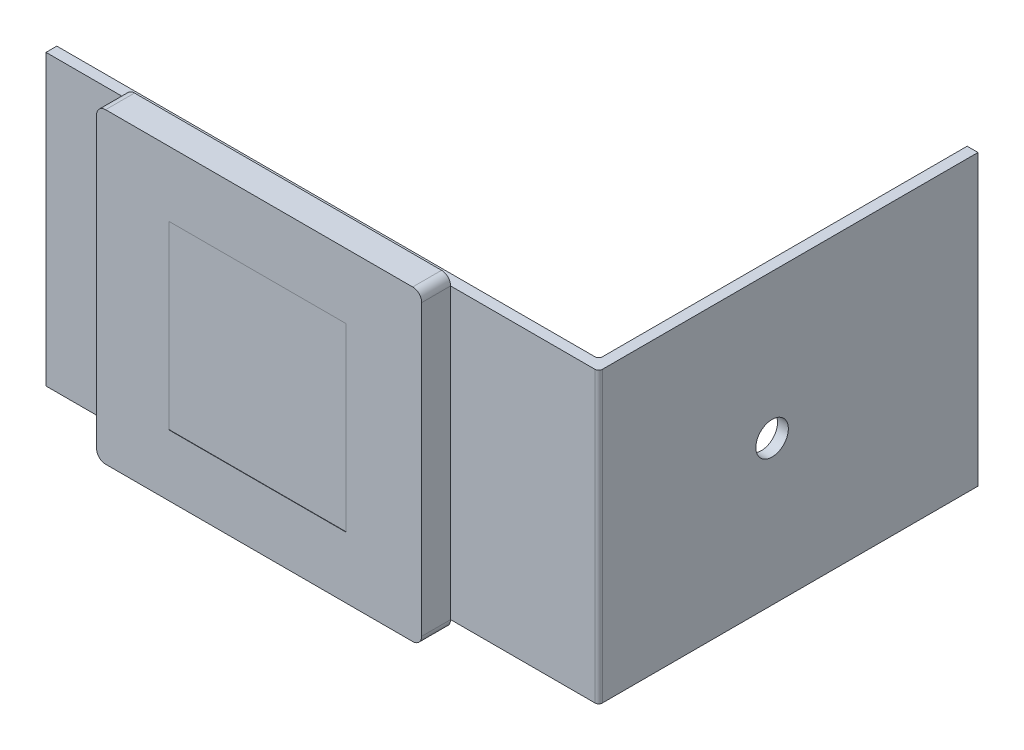
SolidWorks part; units mm, degrees
ref_plane "Ebene vorne" through (0, 0, 0) normal (0, 0, 1) x (1, 0, 0)
ref_plane "Ebene oben" through (0, 0, 0) normal (0, 1, 0) x (1, 0, 0)
ref_plane "Ebene rechts" through (0, 0, 0) normal (1, 0, 0) x (0, 0, -1)
sketch "Skizze1" plane through (0, 0, 0) normal (0, 1, 0) x (1, 0, 0)
  line L0 (-154.7975, -7.5838) -> (-154.7975, -10.5838)
  line L1 (-154.7975, -10.5838) -> (-2.7975, -10.5838)
  line L2 (-1.7975, -9.5838) -> (-1.7975, 94.4162)
  line L3 (-1.7975, 94.4162) -> (-4.7975, 94.4162)
  line L4 (-4.7975, 94.4162) -> (-4.7975, -6.5838)
  line L5 (-5.7975, -7.5838) -> (-154.7975, -7.5838)
  arc A0 (-4.7975, -6.5838) -> (-5.7975, -7.5838) centre (-5.7975, -6.5838) cw
  arc A1 (-2.7975, -10.5838) -> (-1.7975, -9.5838) centre (-2.7975, -9.5838) ccw
  dimension "D1" = 1
  dimension "D2" = 1
  dimension "D3" = 3
  dimension "D4" = 150
  dimension "D5" = 102
extrude "Aufsatz-Linear austragen1" add sketch "Skizze1" along normal blind 80
sketch "Skizze2" plane through (0, 0, 10.5838) normal (0, 0, 1) x (1, 0, 0)
  line L0 (-154.7975, 0) -> (-2.7975, 0) construction
  line L1 (-45.2975, -2.5) -> (-130.2975, -2.5)
  line L2 (-42.7975, 0) -> (-42.7975, 80)
  line L3 (-45.2975, 82.5) -> (-130.2975, 82.5)
  line L4 (-132.7975, 0) -> (-132.7975, 80)
  line L5 (-1.7975, 80) -> (-1.7975, 0) construction
  line L6 (-154.7975, 80) -> (-2.7975, 80) construction
  arc A0 (-45.2975, -2.5) -> (-42.7975, 0) centre (-45.2975, 0) ccw
  arc A1 (-130.2975, -2.5) -> (-132.7975, 0) centre (-130.2975, 0) cw
  arc A2 (-42.7975, 80) -> (-45.2975, 82.5) centre (-45.2975, 80) ccw
  arc A3 (-130.2975, 82.5) -> (-132.7975, 80) centre (-130.2975, 80) ccw
  point P8 (-42.7975, 0)
  dimension "D1" = 2.5
  dimension "D2" = 41
  dimension "D3" = 90
  dimension "D4" = 85
  dimension "D5" = 2.5
extrude "Aufsatz-Linear austragen2" add sketch "Skizze2" along normal blind 8
sketch "Skizze3" plane through (0, 0, 18.5838) normal (0, 0, 1) x (1, 0, 0)
  line L0 (-42.7975, 0) -> (-42.7975, 80) construction
  line L1 (-112.7975, 64.5) -> (-63.7975, 64.5)
  line L2 (-112.7975, 64.5) -> (-112.7975, 14.5)
  line L3 (-112.7975, 14.5) -> (-63.7975, 14.5)
  line L4 (-63.7975, 64.5) -> (-63.7975, 14.5)
  line L5 (-130.2975, -2.5) -> (-45.2975, -2.5) construction
  dimension "D1" = 49
  dimension "D2" = 21
  dimension "D3" = 17
  dimension "D4" = 50
extrude "Aufsatz-Linear austragen4" add sketch "Skizze3" against normal blind 0.1 and the other way blind 0.5 separate body contours L1 L4 L3 L2
combine bodies "Kombinieren1" operation type subtract main body 102 bodies to subtract 104
hole_wizard "Durchgangsloch für M81" positions "Skizze8" profile "Skizze9" hole size "M8" standard "ANSI Metrisch"
sketch "Skizze8" plane through (-1.7975, 0, 0) normal (1, 0, 0) x (0, 0, -1)
  line L0 (-9.5838, 80) -> (94.4162, 80) construction
  line L1 (-9.5838, 80) -> (-9.5838, 0) construction
  point P0 (37.4162, 40)
  dimension "D1" = 40
  dimension "D2" = 47
sketch "Skizze9" plane through (-1.7975, 40, -37.4162) normal (0, 1, 0) x (0, 0, -1)
  line L0 (0, 0) -> (0, 5.7029)
  line L1 (0, 5.7029) -> (4.5, 2.999)
  line L2 (4.5, 2.999) -> (4.5, 0)
  line L5 (4.5, 0) -> (0, 0)
  line L10 (0, 5.7029) -> (-4.5, 2.999) construction
  line L11 (0, -6.35) -> (0, 107.95) construction
  dimension "Bohrerdurchmesser" = 9
  dimension "Bohrungstiefe" = 2.999
  dimension "Spitzenwinkel" = 118
